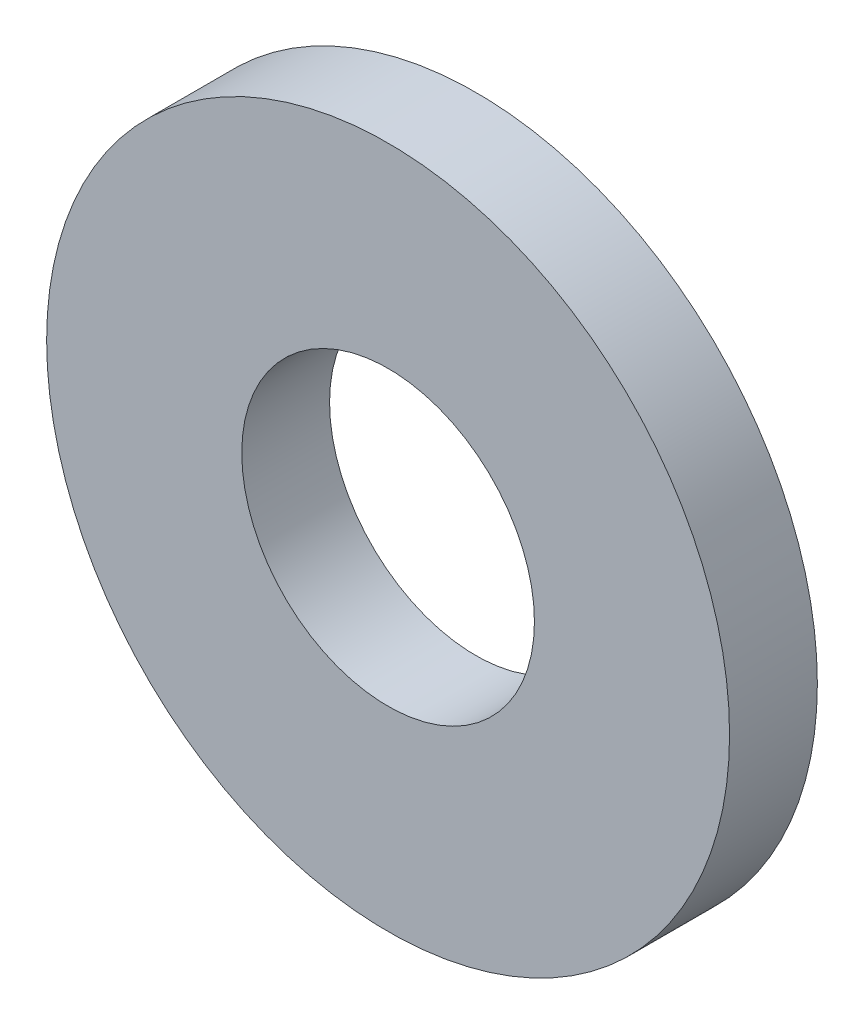
SolidWorks part; units mm, degrees
ref_plane "Front" through (0, 0, 0) normal (0, 0, 1) x (1, 0, 0)
ref_plane "Top" through (0, 0, 0) normal (0, 1, 0) x (1, 0, 0)
ref_plane "Right" through (0, 0, 0) normal (1, 0, 0) x (0, 0, -1)
sketch "Sketch1" plane through (0, 0, 0) normal (0, 0, 1) x (1, 0, 0)
  circle A0 centre (0, 0) radius 1.5
  circle A1 centre (0, 0) radius 3.5
  dimension "D1" = 3
  dimension "D2" = 2
extrude "Boss-Extrude1" add sketch "Sketch1" along normal mid plane 0.9
